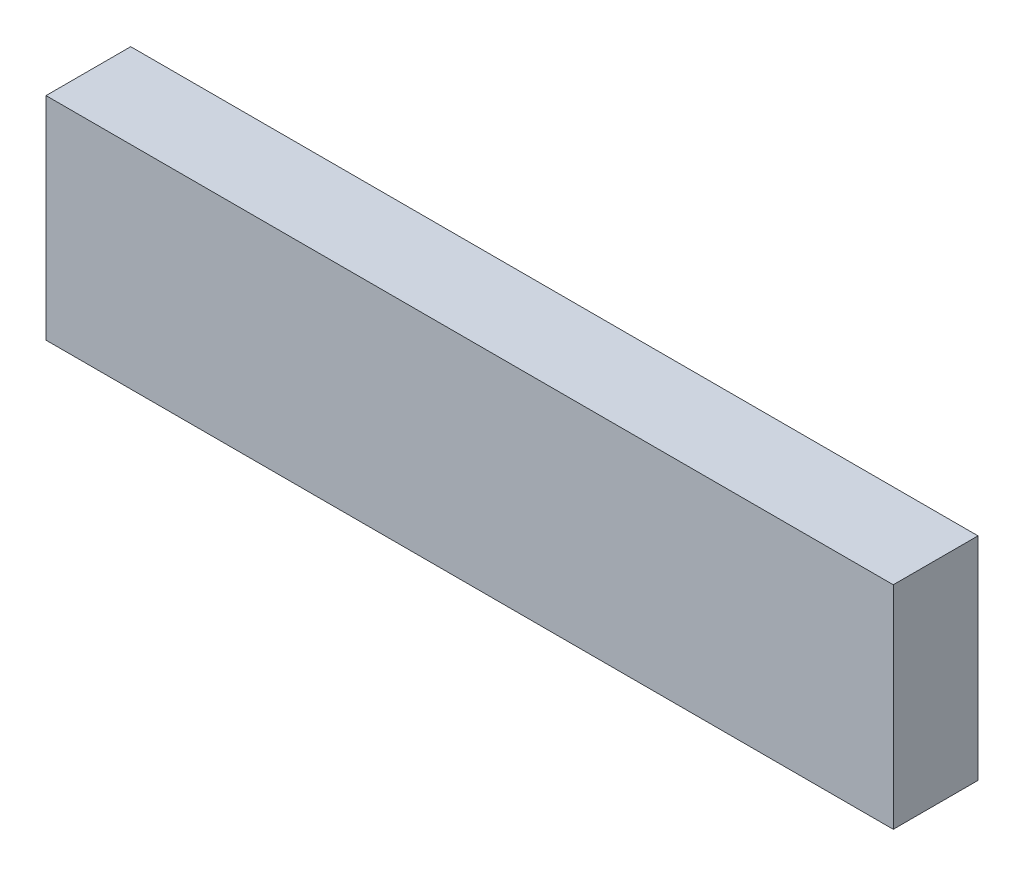
SolidWorks part; units mm, degrees
ref_plane "Front Plane" through (0, 0, 0) normal (0, 0, 1) x (1, 0, 0)
ref_plane "Top Plane" through (0, 0, 0) normal (0, 1, 0) x (1, 0, 0)
ref_plane "Right Plane" through (0, 0, 0) normal (1, 0, 0) x (0, 0, -1)
sketch "Sketch1" plane through (0, 0, 0) normal (0, 1, 0) x (1, 0, 0)
  line L1 (-500, -50) -> (500, -50)
  line L2 (-500, -50) -> (-500, 50)
  line L3 (-500, 50) -> (500, 50)
  line L4 (500, -50) -> (500, 50)
  line L5 (-500, -50) -> (500, 50) construction
  line L6 (-500, 50) -> (500, -50) construction
  point P0 (0, 0)
  dimension "D1" = 1000
  dimension "D2" = 100
extrude "Boss-Extrude1" add sketch "Sketch1" against normal blind 250
